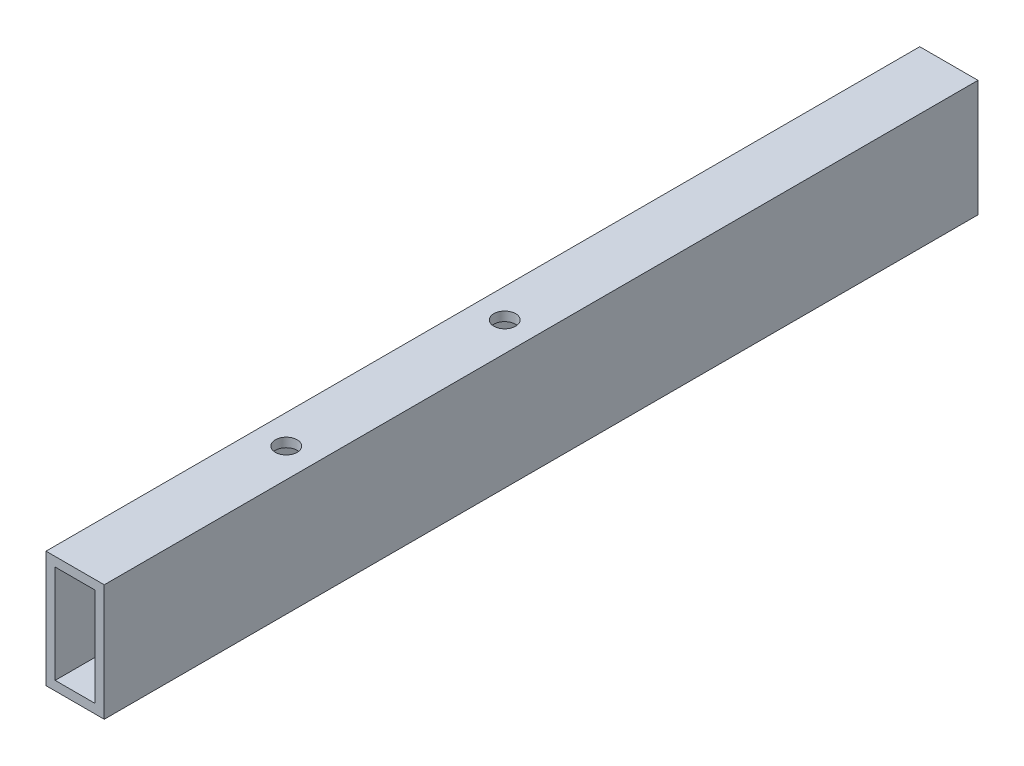
SolidWorks part; units mm, degrees
material "1.0037 (S235JR)"
ref_plane "Front Plane" through (0, 0, 0) normal (0, 0, 1) x (1, 0, 0)
ref_plane "Top Plane" through (0, 0, 0) normal (0, 1, 0) x (1, 0, 0)
ref_plane "Right Plane" through (0, 0, 0) normal (1, 0, 0) x (0, 0, -1)
curve "Curve1"
  spline degree 1 poles (0, 0, -300) (0, 0, 300) knots 0 0 1 1
sketch "Sketch1" plane through (0, 0, 0) normal (0, 0, 1) x (1, 0, 0)
  line L0 (0, 35.3535) -> (0, -33.8384) construction
  line L1 (-20, 40) -> (20, 40)
  line L2 (-20, 40) -> (-20, -40)
  line L3 (-20, -40) -> (20, -40)
  line L4 (20, 40) -> (20, -40)
  line L5 (-13.7, 33.7) -> (13.7, 33.7)
  line L6 (-13.7, 33.7) -> (-13.7, -33.7)
  line L7 (-13.7, -33.7) -> (13.7, -33.7)
  line L8 (13.7, 33.7) -> (13.7, -33.7)
  line L9 (-39.3939, 0) -> (41.5152, 0) construction
  dimension "D1" = 40
  dimension "D2" = 27.4
  dimension "D3" = 80
  dimension "D4" = 67.4
sweep "Sweep1" add profiles "Sketch1" path "Curve1"
hole_wizard "M12 Clearance Hole1" positions "Sketch3" profile "Sketch4" hole size "M12" standard "ISO" end condition through all
sketch "Sketch3" plane through (0, 40, 0) normal (0, 1, 0) x (1, 0, 0)
  line L0 (-20, -300) -> (20, -300) construction
  point P9 (0, -155)
  point P11 (0, -5)
  dimension "D1" = 150
  dimension "D2" = 145
sketch "Sketch4" plane through (0, 40, 155) normal (1, 0, 0) x (0, 0, 1)
  line L0 (0, 0) -> (0, 80)
  line L1 (0, 80) -> (7.5, 80)
  line L2 (7.5, 80) -> (7.5, 0)
  line L5 (7.5, 0) -> (0, 0)
  line L11 (0, -6.35) -> (0, 107.95) construction
  dimension "Thru Hole Dia." = 15
  dimension "Thru Hole Depth" = 80
